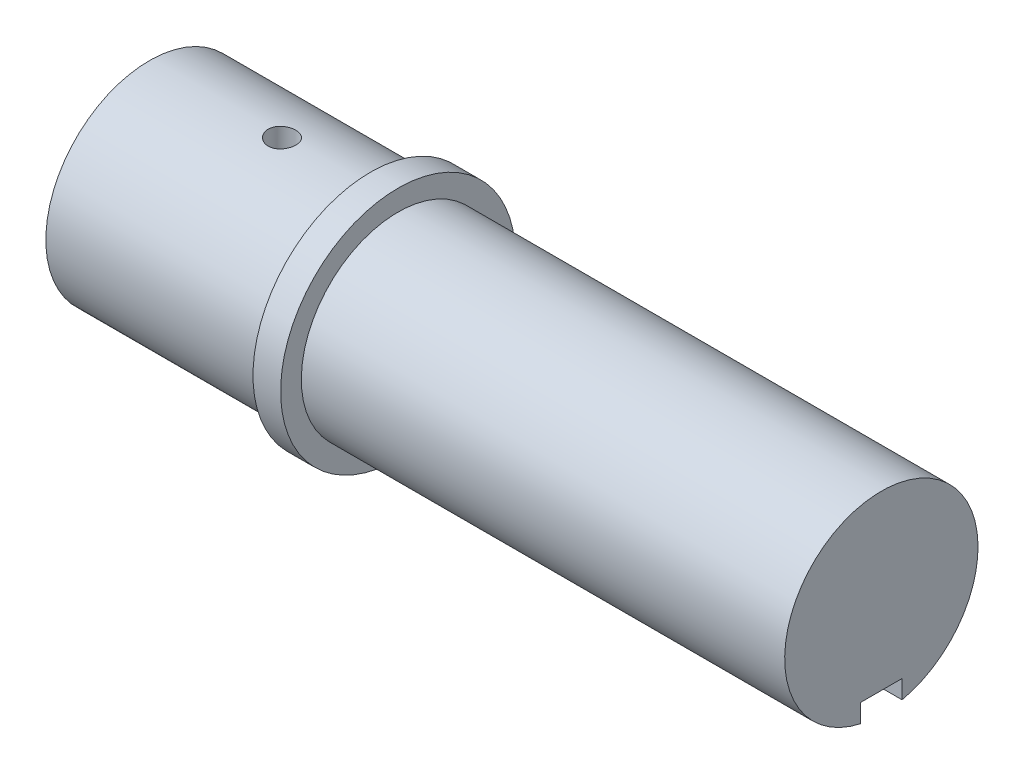
SolidWorks part; units mm, degrees
material "Plain Carbon Steel"
ref_plane "Front Plane" through (0, 0, 0) normal (0, 0, 1) x (1, 0, 0)
ref_plane "Top Plane" through (0, 0, 0) normal (0, 1, 0) x (1, 0, 0)
ref_plane "Right Plane" through (0, 0, 0) normal (1, 0, 0) x (0, 0, -1)
sketch "Sketch1" plane through (0, 0, 0) normal (1, 0, 0) x (0, 0, -1)
  circle A0 centre (0, 0) radius 7.5
  dimension "D1" = 15
extrude "Boss-Extrude1" add sketch "Sketch1" along normal blind 16
sketch "Sketch2" plane through (16, 0, 0) normal (1, 0, 0) x (0, 0, -1)
  circle A0 centre (0, 0) radius 8.5
  dimension "D1" = 17
extrude "Boss-Extrude2" add sketch "Sketch2" along normal blind 2
sketch "Sketch3" plane through (18, 0, 0) normal (1, 0, 0) x (0, 0, -1)
  circle A0 centre (0, 0) radius 7
  dimension "D1" = 14
extrude "Boss-Extrude3" add sketch "Sketch3" along normal blind 35
sketch "Sketch4" plane through (0, 0, 0) normal (-1, 0, 0) x (0, 0, 1)
  circle A0 centre (0, 0) radius 4
  dimension "D1" = 8
extrude "Cut-Extrude1" cut sketch "Sketch4" against normal blind 20.5
sketch "Sketch6" plane through (0, 0, 0) normal (-1, 0, 0) x (0, 0, 1)
  line L0 (0, -9.35) -> (0, 9.35) construction
  line L1 (-1.5, 3.25) -> (1.5, 3.25)
  line L2 (-1.5, 3.25) -> (-1.5, 4.75)
  line L3 (-1.5, 4.75) -> (1.5, 4.75)
  line L4 (1.5, 3.25) -> (1.5, 4.75)
  line L5 (-1.5, 3.25) -> (1.5, 4.75) construction
  line L6 (-1.5, 4.75) -> (1.5, 3.25) construction
  circle A0 centre (0, 0) radius 4 construction
  point P0 (0, 4)
  dimension "D1" = 3
  dimension "D2" = 1.5
extrude "Cut-Extrude2" cut sketch "Sketch6" against normal blind 20.5
ref_plane "Plane1" through (0, 7.5, 0) normal (0, 1, 0) x (1, 0, 0)
sketch "Sketch7" plane through (0, 7.5, 0) normal (0, 1, 0) x (1, 0, 0)
  line L0 (-9.35, 0) -> (9.35, 0) construction
  line L1 (0, -9.35) -> (0, 9.35) construction
  circle A0 centre (9.6, 0) radius 1
  dimension "D1" = 2
  dimension "D2" = 9.6
extrude "Cut-Extrude3" cut sketch "Sketch7" against normal up to next
sketch "Sketch8" plane through (53, 0, 0) normal (1, 0, 0) x (0, 0, -1)
  line L0 (0, 9.35) -> (0, -9.35) construction
  line L1 (-1.5, -8.5) -> (1.5, -8.5)
  line L2 (-1.5, -8.5) -> (-1.5, -5.5)
  line L3 (-1.5, -5.5) -> (1.5, -5.5)
  line L4 (1.5, -8.5) -> (1.5, -5.5)
  line L5 (-1.5, -8.5) -> (1.5, -5.5) construction
  line L6 (-1.5, -5.5) -> (1.5, -8.5) construction
  circle A0 centre (0, 0) radius 7 construction
  point P0 (0, -7)
  dimension "D1" = 3
  dimension "D2" = 1.5
extrude "Cut-Extrude5" cut sketch "Sketch8" against normal blind 33
